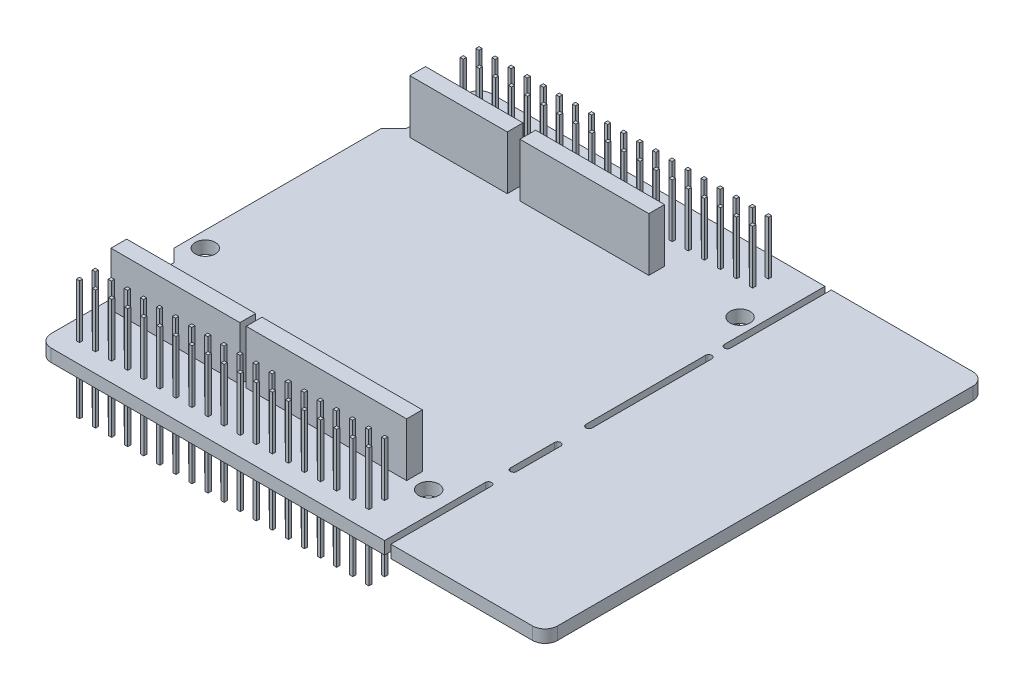
SolidWorks part; units mm, degrees
ref_plane "Płaszczyzna przednia" through (0, 0, 0) normal (0, 0, 1) x (1, 0, 0)
ref_plane "Płaszczyzna górna" through (0, 0, 0) normal (0, 1, 0) x (1, 0, 0)
ref_plane "Płaszczyzna prawa" through (0, 0, 0) normal (1, 0, 0) x (0, 0, -1)
sketch "Szkic2" plane through (0, 0, 0) normal (0, 1, 0) x (1, 0, 0)
  line L0 (-43.3193, -7.1981) -> (-41.3193, -9.1981)
  line L1 (-41.3193, -9.1981) -> (-41.3193, -28.6981)
  line L2 (-39.3193, -30.6981) -> (37.1807, -30.6981)
  line L3 (39.1807, -28.6981) -> (39.1807, 37.3019)
  line L4 (37.1807, 39.3019) -> (-39.3193, 39.3019)
  line L5 (-41.3193, 37.3019) -> (-41.3193, 27.8019)
  line L6 (-41.3193, 27.8019) -> (-43.3193, 25.8019)
  line L7 (-43.3193, 25.8019) -> (-43.3193, -7.1981)
  line L8 (14.1807, 39.3019) -> (14.1807, 23.3019) construction
  line L9 (14.6807, 39.3019) -> (14.6807, 23.3019)
  line L10 (13.6807, 39.3019) -> (13.6807, 23.3019)
  line L11 (14.1807, 20.3019) -> (14.1807, 1.3019) construction
  line L12 (14.6807, 20.3019) -> (14.6807, 1.3019)
  line L13 (13.6807, 20.3019) -> (13.6807, 1.3019)
  line L14 (14.1807, -3.6981) -> (14.1807, -10.6981) construction
  line L15 (14.6807, -3.6981) -> (14.6807, -10.6981)
  line L16 (13.6807, -3.6981) -> (13.6807, -10.6981)
  line L17 (14.1807, -14.6981) -> (14.1807, -30.6981) construction
  line L18 (14.6807, -14.6981) -> (14.6807, -30.6981)
  line L19 (13.6807, -14.6981) -> (13.6807, -30.6981)
  arc A0 (-41.3193, -28.6981) -> (-39.3193, -30.6981) centre (-39.3193, -28.6981) ccw
  arc A1 (37.1807, -30.6981) -> (39.1807, -28.6981) centre (37.1807, -28.6981) ccw
  arc A2 (39.1807, 37.3019) -> (37.1807, 39.3019) centre (37.1807, 37.3019) ccw
  arc A3 (-39.3193, 39.3019) -> (-41.3193, 37.3019) centre (-39.3193, 37.3019) ccw
  arc A4 (14.6807, 39.3019) -> (13.6807, 39.3019) centre (14.1807, 39.3019) ccw
  arc A5 (13.6807, 23.3019) -> (14.6807, 23.3019) centre (14.1807, 23.3019) ccw
  arc A6 (14.6807, 20.3019) -> (13.6807, 20.3019) centre (14.1807, 20.3019) ccw
  arc A7 (13.6807, 1.3019) -> (14.6807, 1.3019) centre (14.1807, 1.3019) ccw
  arc A8 (14.6807, -3.6981) -> (13.6807, -3.6981) centre (14.1807, -3.6981) ccw
  arc A9 (13.6807, -10.6981) -> (14.6807, -10.6981) centre (14.1807, -10.6981) ccw
  arc A10 (14.6807, -14.6981) -> (13.6807, -14.6981) centre (14.1807, -14.6981) ccw
  arc A11 (13.6807, -30.6981) -> (14.6807, -30.6981) centre (14.1807, -30.6981) ccw
  circle A12 centre (10.1807, -20.1981) radius 1.6
  circle A13 centre (11.1807, 28.3019) radius 1.6
  circle A14 centre (-40.8193, -4.6981) radius 1.6
  point P2 (14.1807, 31.3019)
  point P25 (14.1807, 10.8019)
  point P32 (14.1807, -7.1981)
  point P37 (14.1807, -22.6981)
  dimension "D4" = 2
  dimension "D8" = 1
  dimension "D16" = 3.2
  dimension "D1" = 80.5
  dimension "D2" = 70
  dimension "D3" = 82.5
  dimension "D5" = 11.5
  dimension "D6" = 135
  dimension "D7" = 21.5
  dimension "D9" = 24.5
  dimension "D10" = 16
  dimension "D11" = 19
  dimension "D12" = 3
  dimension "D13" = 5
  dimension "D14" = 7
  dimension "D15" = 4
  dimension "D17" = 2.5
  dimension "D18" = 26
  dimension "D19" = 10.5
  dimension "D20" = 53.5
  dimension "D21" = 54.5
  dimension "D22" = 11
extrude "Dodanie-wyciągnięcie1" add sketch "Szkic2" along normal blind 2 contours A10 L18 L2 A1 L3 A2 L4 L9 A5 L10 A3 L5 L6 L7 L0 L1 A0 L19 A14 A13 A12 A9 L16 A8 L15 A7 L13 A6 L12
sketch "Szkic3" plane through (0, 2, 0) normal (0, 1, 0) x (1, 0, 0)
  line L0 (-41.3193, -9.1981) -> (-41.3193, -28.6981) construction
  line L1 (-39.8193, 26.8019) -> (-24.3193, 26.8019)
  line L2 (-39.8193, 26.8019) -> (-39.8193, 29.3019)
  line L3 (-39.8193, 29.3019) -> (-24.3193, 29.3019)
  line L4 (-24.3193, 26.8019) -> (-24.3193, 29.3019)
  line L5 (-22.3193, 26.8019) -> (-1.8193, 26.8019)
  line L6 (-22.3193, 26.8019) -> (-22.3193, 29.3019)
  line L7 (-22.3193, 29.3019) -> (-1.8193, 29.3019)
  line L8 (-1.8193, 26.8019) -> (-1.8193, 29.3019)
  line L9 (-39.8193, -20.6981) -> (-19.3193, -20.6981)
  line L10 (-39.8193, -20.6981) -> (-39.8193, -18.1981)
  line L11 (-39.8193, -18.1981) -> (-19.3193, -18.1981)
  line L12 (-19.3193, -20.6981) -> (-19.3193, -18.1981)
  line L13 (-18.3193, -20.6981) -> (7.1807, -20.6981)
  line L14 (-18.3193, -20.6981) -> (-18.3193, -18.1981)
  line L15 (-18.3193, -18.1981) -> (7.1807, -18.1981)
  line L16 (7.1807, -20.6981) -> (7.1807, -18.1981)
  line L18 (13.6807, 39.3019) -> (-39.3193, 39.3019) construction
  line L19 (-39.3193, -30.6981) -> (13.6807, -30.6981) construction
  dimension "D1" = 2.5
  dimension "D2" = 15.5
  dimension "D3" = 2.5
  dimension "D4" = 20.5
  dimension "D5" = 2.5
  dimension "D6" = 20.5
  dimension "D7" = 2.5
  dimension "D8" = 25.5
  dimension "D9" = 1.5
  dimension "D10" = 1
  dimension "D11" = 2
  dimension "D12" = 10
  dimension "D13" = 10
extrude "Dodanie-wyciągnięcie2" add sketch "Szkic3" along normal blind 8.5
sketch "Szkic4" plane through (0, 0, 0) normal (0, -1, 0) x (-1, 0, 0)
  line L8 (-9.1807, 32.3019) -> (39.3193, 32.3019) construction
  line L9 (-9.1807, 32.3019) -> (-9.1807, 37.3019) construction
  line L10 (-9.1807, 37.3019) -> (39.3193, 37.3019) construction
  line L11 (39.3193, 32.3019) -> (39.3193, 37.3019) construction
  line L12 (-13.6807, 39.3019) -> (39.3193, 39.3019) construction
  line L165 (-9.1807, 34.8019) -> (39.3193, 34.8019) construction
  line L166 (-8.1807, 35.8019) -> (-7.6807, 35.8019)
  line L167 (-8.1807, 35.8019) -> (-8.1807, 36.3019)
  line L168 (-8.1807, 36.3019) -> (-7.6807, 36.3019)
  line L169 (-7.6807, 35.8019) -> (-7.6807, 36.3019)
  line L170 (-8.1807, 33.3019) -> (-7.6807, 33.3019)
  line L171 (-8.1807, 33.3019) -> (-8.1807, 33.8019)
  line L172 (-8.1807, 33.8019) -> (-7.6807, 33.8019)
  line L173 (-7.6807, 33.3019) -> (-7.6807, 33.8019)
  line L174 (-5.6251, 35.8019) -> (-5.6251, 36.3019)
  line L176 (-5.6251, 35.8019) -> (-5.1251, 35.8019)
  line L177 (-5.1251, 35.8019) -> (-5.1251, 36.3019)
  line L178 (-5.6251, 36.3019) -> (-5.1251, 36.3019)
  line L179 (-5.6251, 33.3019) -> (-5.6251, 33.8019)
  line L180 (-5.6251, 33.3019) -> (-5.1251, 33.3019)
  line L181 (-5.1251, 33.3019) -> (-5.1251, 33.8019)
  line L182 (-5.6251, 33.8019) -> (-5.1251, 33.8019)
  line L183 (-3.0696, 35.8019) -> (-3.0696, 36.3019)
  line L184 (-3.0696, 35.8019) -> (-2.5696, 35.8019)
  line L185 (-2.5696, 35.8019) -> (-2.5696, 36.3019)
  line L186 (-3.0696, 36.3019) -> (-2.5696, 36.3019)
  line L187 (-3.0696, 33.3019) -> (-3.0696, 33.8019)
  line L188 (-3.0696, 33.3019) -> (-2.5696, 33.3019)
  line L189 (-2.5696, 33.3019) -> (-2.5696, 33.8019)
  line L190 (-3.0696, 33.8019) -> (-2.5696, 33.8019)
  line L191 (-0.514, 35.8019) -> (-0.514, 36.3019)
  line L192 (-0.514, 35.8019) -> (-0.014, 35.8019)
  line L193 (-0.014, 35.8019) -> (-0.014, 36.3019)
  line L194 (-0.514, 36.3019) -> (-0.014, 36.3019)
  line L195 (-0.514, 33.3019) -> (-0.514, 33.8019)
  line L196 (-0.514, 33.3019) -> (-0.014, 33.3019)
  line L197 (-0.014, 33.3019) -> (-0.014, 33.8019)
  line L198 (-0.514, 33.8019) -> (-0.014, 33.8019)
  line L199 (2.0415, 35.8019) -> (2.0415, 36.3019)
  line L200 (2.0415, 35.8019) -> (2.5415, 35.8019)
  line L201 (2.5415, 35.8019) -> (2.5415, 36.3019)
  line L202 (2.0415, 36.3019) -> (2.5415, 36.3019)
  line L203 (2.0415, 33.3019) -> (2.0415, 33.8019)
  line L204 (2.0415, 33.3019) -> (2.5415, 33.3019)
  line L205 (2.5415, 33.3019) -> (2.5415, 33.8019)
  line L206 (2.0415, 33.8019) -> (2.5415, 33.8019)
  line L207 (4.5971, 35.8019) -> (4.5971, 36.3019)
  line L208 (4.5971, 35.8019) -> (5.0971, 35.8019)
  line L209 (5.0971, 35.8019) -> (5.0971, 36.3019)
  line L210 (4.5971, 36.3019) -> (5.0971, 36.3019)
  line L211 (4.5971, 33.3019) -> (4.5971, 33.8019)
  line L212 (4.5971, 33.3019) -> (5.0971, 33.3019)
  line L213 (5.0971, 33.3019) -> (5.0971, 33.8019)
  line L214 (4.5971, 33.8019) -> (5.0971, 33.8019)
  line L215 (7.1526, 35.8019) -> (7.1526, 36.3019)
  line L216 (7.1526, 35.8019) -> (7.6526, 35.8019)
  line L217 (7.6526, 35.8019) -> (7.6526, 36.3019)
  line L218 (7.1526, 36.3019) -> (7.6526, 36.3019)
  line L219 (7.1526, 33.3019) -> (7.1526, 33.8019)
  line L220 (7.1526, 33.3019) -> (7.6526, 33.3019)
  line L221 (7.6526, 33.3019) -> (7.6526, 33.8019)
  line L222 (7.1526, 33.8019) -> (7.6526, 33.8019)
  line L223 (9.7082, 35.8019) -> (9.7082, 36.3019)
  line L224 (9.7082, 35.8019) -> (10.2082, 35.8019)
  line L225 (10.2082, 35.8019) -> (10.2082, 36.3019)
  line L226 (9.7082, 36.3019) -> (10.2082, 36.3019)
  line L227 (9.7082, 33.3019) -> (9.7082, 33.8019)
  line L228 (9.7082, 33.3019) -> (10.2082, 33.3019)
  line L229 (10.2082, 33.3019) -> (10.2082, 33.8019)
  line L230 (9.7082, 33.8019) -> (10.2082, 33.8019)
  line L231 (12.2637, 35.8019) -> (12.2637, 36.3019)
  line L232 (12.2637, 35.8019) -> (12.7637, 35.8019)
  line L233 (12.7637, 35.8019) -> (12.7637, 36.3019)
  line L234 (12.2637, 36.3019) -> (12.7637, 36.3019)
  line L235 (12.2637, 33.3019) -> (12.2637, 33.8019)
  line L236 (12.2637, 33.3019) -> (12.7637, 33.3019)
  line L237 (12.7637, 33.3019) -> (12.7637, 33.8019)
  line L238 (12.2637, 33.8019) -> (12.7637, 33.8019)
  line L239 (14.8193, 35.8019) -> (14.8193, 36.3019)
  line L240 (14.8193, 35.8019) -> (15.3193, 35.8019)
  line L241 (15.3193, 35.8019) -> (15.3193, 36.3019)
  line L242 (14.8193, 36.3019) -> (15.3193, 36.3019)
  line L243 (14.8193, 33.3019) -> (14.8193, 33.8019)
  line L244 (14.8193, 33.3019) -> (15.3193, 33.3019)
  line L245 (15.3193, 33.3019) -> (15.3193, 33.8019)
  line L246 (14.8193, 33.8019) -> (15.3193, 33.8019)
  line L247 (17.3749, 35.8019) -> (17.3749, 36.3019)
  line L248 (17.3749, 35.8019) -> (17.8749, 35.8019)
  line L249 (17.8749, 35.8019) -> (17.8749, 36.3019)
  line L250 (17.3749, 36.3019) -> (17.8749, 36.3019)
  line L251 (17.3749, 33.3019) -> (17.3749, 33.8019)
  line L252 (17.3749, 33.3019) -> (17.8749, 33.3019)
  line L253 (17.8749, 33.3019) -> (17.8749, 33.8019)
  line L254 (17.3749, 33.8019) -> (17.8749, 33.8019)
  line L255 (19.9304, 35.8019) -> (19.9304, 36.3019)
  line L256 (19.9304, 35.8019) -> (20.4304, 35.8019)
  line L257 (20.4304, 35.8019) -> (20.4304, 36.3019)
  line L258 (19.9304, 36.3019) -> (20.4304, 36.3019)
  line L259 (19.9304, 33.3019) -> (19.9304, 33.8019)
  line L260 (19.9304, 33.3019) -> (20.4304, 33.3019)
  line L261 (20.4304, 33.3019) -> (20.4304, 33.8019)
  line L262 (19.9304, 33.8019) -> (20.4304, 33.8019)
  line L263 (22.486, 35.8019) -> (22.486, 36.3019)
  line L264 (22.486, 35.8019) -> (22.986, 35.8019)
  line L265 (22.986, 35.8019) -> (22.986, 36.3019)
  line L266 (22.486, 36.3019) -> (22.986, 36.3019)
  line L267 (22.486, 33.3019) -> (22.486, 33.8019)
  line L268 (22.486, 33.3019) -> (22.986, 33.3019)
  line L269 (22.986, 33.3019) -> (22.986, 33.8019)
  line L270 (22.486, 33.8019) -> (22.986, 33.8019)
  line L271 (25.0415, 35.8019) -> (25.0415, 36.3019)
  line L272 (25.0415, 35.8019) -> (25.5415, 35.8019)
  line L273 (25.5415, 35.8019) -> (25.5415, 36.3019)
  line L274 (25.0415, 36.3019) -> (25.5415, 36.3019)
  line L275 (25.0415, 33.3019) -> (25.0415, 33.8019)
  line L276 (25.0415, 33.3019) -> (25.5415, 33.3019)
  line L277 (25.5415, 33.3019) -> (25.5415, 33.8019)
  line L278 (25.0415, 33.8019) -> (25.5415, 33.8019)
  line L279 (27.5971, 35.8019) -> (27.5971, 36.3019)
  line L280 (27.5971, 35.8019) -> (28.0971, 35.8019)
  line L281 (28.0971, 35.8019) -> (28.0971, 36.3019)
  line L282 (27.5971, 36.3019) -> (28.0971, 36.3019)
  line L283 (27.5971, 33.3019) -> (27.5971, 33.8019)
  line L284 (27.5971, 33.3019) -> (28.0971, 33.3019)
  line L285 (28.0971, 33.3019) -> (28.0971, 33.8019)
  line L286 (27.5971, 33.8019) -> (28.0971, 33.8019)
  line L287 (30.1526, 35.8019) -> (30.1526, 36.3019)
  line L288 (30.1526, 35.8019) -> (30.6526, 35.8019)
  line L289 (30.6526, 35.8019) -> (30.6526, 36.3019)
  line L290 (30.1526, 36.3019) -> (30.6526, 36.3019)
  line L291 (30.1526, 33.3019) -> (30.1526, 33.8019)
  line L292 (30.1526, 33.3019) -> (30.6526, 33.3019)
  line L293 (30.6526, 33.3019) -> (30.6526, 33.8019)
  line L294 (30.1526, 33.8019) -> (30.6526, 33.8019)
  line L295 (32.7082, 35.8019) -> (32.7082, 36.3019)
  line L296 (32.7082, 35.8019) -> (33.2082, 35.8019)
  line L297 (33.2082, 35.8019) -> (33.2082, 36.3019)
  line L298 (32.7082, 36.3019) -> (33.2082, 36.3019)
  line L299 (32.7082, 33.3019) -> (32.7082, 33.8019)
  line L300 (32.7082, 33.3019) -> (33.2082, 33.3019)
  line L301 (33.2082, 33.3019) -> (33.2082, 33.8019)
  line L302 (32.7082, 33.8019) -> (33.2082, 33.8019)
  line L303 (35.2637, 35.8019) -> (35.2637, 36.3019)
  line L304 (35.2637, 35.8019) -> (35.7637, 35.8019)
  line L305 (35.7637, 35.8019) -> (35.7637, 36.3019)
  line L306 (35.2637, 36.3019) -> (35.7637, 36.3019)
  line L307 (35.2637, 33.3019) -> (35.2637, 33.8019)
  line L308 (35.2637, 33.3019) -> (35.7637, 33.3019)
  line L309 (35.7637, 33.3019) -> (35.7637, 33.8019)
  line L310 (35.2637, 33.8019) -> (35.7637, 33.8019)
  line L311 (37.8193, 35.8019) -> (37.8193, 36.3019)
  line L312 (37.8193, 35.8019) -> (38.3193, 35.8019)
  line L313 (38.3193, 35.8019) -> (38.3193, 36.3019)
  line L314 (37.8193, 36.3019) -> (38.3193, 36.3019)
  line L315 (37.8193, 33.3019) -> (37.8193, 33.8019)
  line L316 (37.8193, 33.3019) -> (38.3193, 33.3019)
  line L317 (38.3193, 33.3019) -> (38.3193, 33.8019)
  line L318 (37.8193, 33.8019) -> (38.3193, 33.8019)
  line L319 (-9.1807, -28.6981) -> (39.3193, -28.6981) construction
  line L320 (-9.1807, -28.6981) -> (-9.1807, -23.6981) construction
  line L321 (-9.1807, -23.6981) -> (39.3193, -23.6981) construction
  line L322 (39.3193, -28.6981) -> (39.3193, -23.6981) construction
  line L323 (-9.1807, -26.1981) -> (39.3193, -26.1981) construction
  line L324 (-8.1807, -25.1981) -> (-7.6807, -25.1981)
  line L325 (-8.1807, -25.1981) -> (-8.1807, -24.6981)
  line L326 (-8.1807, -24.6981) -> (-7.6807, -24.6981)
  line L327 (-7.6807, -25.1981) -> (-7.6807, -24.6981)
  line L328 (-8.1807, -27.6981) -> (-7.6807, -27.6981)
  line L329 (-8.1807, -27.6981) -> (-8.1807, -27.1981)
  line L330 (-8.1807, -27.1981) -> (-7.6807, -27.1981)
  line L331 (-7.6807, -27.6981) -> (-7.6807, -27.1981)
  line L332 (-5.6251, -25.1981) -> (-5.6251, -24.6981)
  line L333 (-5.6251, -25.1981) -> (-5.1251, -25.1981)
  line L334 (-5.1251, -25.1981) -> (-5.1251, -24.6981)
  line L335 (-5.6251, -24.6981) -> (-5.1251, -24.6981)
  line L336 (-5.6251, -27.6981) -> (-5.6251, -27.1981)
  line L337 (-5.6251, -27.6981) -> (-5.1251, -27.6981)
  line L338 (-5.1251, -27.6981) -> (-5.1251, -27.1981)
  line L339 (-5.6251, -27.1981) -> (-5.1251, -27.1981)
  line L340 (-3.0696, -25.1981) -> (-3.0696, -24.6981)
  line L341 (-3.0696, -25.1981) -> (-2.5696, -25.1981)
  line L342 (-2.5696, -25.1981) -> (-2.5696, -24.6981)
  line L343 (-3.0696, -24.6981) -> (-2.5696, -24.6981)
  line L344 (-3.0696, -27.6981) -> (-3.0696, -27.1981)
  line L345 (-3.0696, -27.6981) -> (-2.5696, -27.6981)
  line L346 (-2.5696, -27.6981) -> (-2.5696, -27.1981)
  line L347 (-3.0696, -27.1981) -> (-2.5696, -27.1981)
  line L348 (-0.514, -25.1981) -> (-0.514, -24.6981)
  line L349 (-0.514, -25.1981) -> (-0.014, -25.1981)
  line L350 (-0.014, -25.1981) -> (-0.014, -24.6981)
  line L351 (-0.514, -24.6981) -> (-0.014, -24.6981)
  line L352 (-0.514, -27.6981) -> (-0.514, -27.1981)
  line L353 (-0.514, -27.6981) -> (-0.014, -27.6981)
  line L354 (-0.014, -27.6981) -> (-0.014, -27.1981)
  line L355 (-0.514, -27.1981) -> (-0.014, -27.1981)
  line L356 (2.0415, -25.1981) -> (2.0415, -24.6981)
  line L357 (2.0415, -25.1981) -> (2.5415, -25.1981)
  line L358 (2.5415, -25.1981) -> (2.5415, -24.6981)
  line L359 (2.0415, -24.6981) -> (2.5415, -24.6981)
  line L360 (2.0415, -27.6981) -> (2.0415, -27.1981)
  line L361 (2.0415, -27.6981) -> (2.5415, -27.6981)
  line L362 (2.5415, -27.6981) -> (2.5415, -27.1981)
  line L363 (2.0415, -27.1981) -> (2.5415, -27.1981)
  line L364 (4.5971, -25.1981) -> (4.5971, -24.6981)
  line L365 (4.5971, -25.1981) -> (5.0971, -25.1981)
  line L366 (5.0971, -25.1981) -> (5.0971, -24.6981)
  line L367 (4.5971, -24.6981) -> (5.0971, -24.6981)
  line L368 (4.5971, -27.6981) -> (4.5971, -27.1981)
  line L369 (4.5971, -27.6981) -> (5.0971, -27.6981)
  line L370 (5.0971, -27.6981) -> (5.0971, -27.1981)
  line L371 (4.5971, -27.1981) -> (5.0971, -27.1981)
  line L372 (7.1526, -25.1981) -> (7.1526, -24.6981)
  line L373 (7.1526, -25.1981) -> (7.6526, -25.1981)
  line L374 (7.6526, -25.1981) -> (7.6526, -24.6981)
  line L375 (7.1526, -24.6981) -> (7.6526, -24.6981)
  line L376 (7.1526, -27.6981) -> (7.1526, -27.1981)
  line L377 (7.1526, -27.6981) -> (7.6526, -27.6981)
  line L378 (7.6526, -27.6981) -> (7.6526, -27.1981)
  line L379 (7.1526, -27.1981) -> (7.6526, -27.1981)
  line L380 (9.7082, -25.1981) -> (9.7082, -24.6981)
  line L381 (9.7082, -25.1981) -> (10.2082, -25.1981)
  line L382 (10.2082, -25.1981) -> (10.2082, -24.6981)
  line L383 (9.7082, -24.6981) -> (10.2082, -24.6981)
  line L384 (9.7082, -27.6981) -> (9.7082, -27.1981)
  line L385 (9.7082, -27.6981) -> (10.2082, -27.6981)
  line L386 (10.2082, -27.6981) -> (10.2082, -27.1981)
  line L387 (9.7082, -27.1981) -> (10.2082, -27.1981)
  line L388 (12.2637, -25.1981) -> (12.2637, -24.6981)
  line L389 (12.2637, -25.1981) -> (12.7637, -25.1981)
  line L390 (12.7637, -25.1981) -> (12.7637, -24.6981)
  line L391 (12.2637, -24.6981) -> (12.7637, -24.6981)
  line L392 (12.2637, -27.6981) -> (12.2637, -27.1981)
  line L393 (12.2637, -27.6981) -> (12.7637, -27.6981)
  line L394 (12.7637, -27.6981) -> (12.7637, -27.1981)
  line L395 (12.2637, -27.1981) -> (12.7637, -27.1981)
  line L396 (14.8193, -25.1981) -> (14.8193, -24.6981)
  line L397 (14.8193, -25.1981) -> (15.3193, -25.1981)
  line L398 (15.3193, -25.1981) -> (15.3193, -24.6981)
  line L399 (14.8193, -24.6981) -> (15.3193, -24.6981)
  line L400 (14.8193, -27.6981) -> (14.8193, -27.1981)
  line L401 (14.8193, -27.6981) -> (15.3193, -27.6981)
  line L402 (15.3193, -27.6981) -> (15.3193, -27.1981)
  line L403 (14.8193, -27.1981) -> (15.3193, -27.1981)
  line L404 (17.3749, -25.1981) -> (17.3749, -24.6981)
  line L405 (17.3749, -25.1981) -> (17.8749, -25.1981)
  line L406 (17.8749, -25.1981) -> (17.8749, -24.6981)
  line L407 (17.3749, -24.6981) -> (17.8749, -24.6981)
  line L408 (17.3749, -27.6981) -> (17.3749, -27.1981)
  line L409 (17.3749, -27.6981) -> (17.8749, -27.6981)
  line L410 (17.8749, -27.6981) -> (17.8749, -27.1981)
  line L411 (17.3749, -27.1981) -> (17.8749, -27.1981)
  line L412 (19.9304, -25.1981) -> (19.9304, -24.6981)
  line L413 (19.9304, -25.1981) -> (20.4304, -25.1981)
  line L414 (20.4304, -25.1981) -> (20.4304, -24.6981)
  line L415 (19.9304, -24.6981) -> (20.4304, -24.6981)
  line L416 (19.9304, -27.6981) -> (19.9304, -27.1981)
  line L417 (19.9304, -27.6981) -> (20.4304, -27.6981)
  line L418 (20.4304, -27.6981) -> (20.4304, -27.1981)
  line L419 (19.9304, -27.1981) -> (20.4304, -27.1981)
  line L420 (22.486, -25.1981) -> (22.486, -24.6981)
  line L421 (22.486, -25.1981) -> (22.986, -25.1981)
  line L422 (22.986, -25.1981) -> (22.986, -24.6981)
  line L423 (22.486, -24.6981) -> (22.986, -24.6981)
  line L424 (22.486, -27.6981) -> (22.486, -27.1981)
  line L425 (22.486, -27.6981) -> (22.986, -27.6981)
  line L426 (22.986, -27.6981) -> (22.986, -27.1981)
  line L427 (22.486, -27.1981) -> (22.986, -27.1981)
  line L428 (25.0415, -25.1981) -> (25.0415, -24.6981)
  line L429 (25.0415, -25.1981) -> (25.5415, -25.1981)
  line L430 (25.5415, -25.1981) -> (25.5415, -24.6981)
  line L431 (25.0415, -24.6981) -> (25.5415, -24.6981)
  line L432 (25.0415, -27.6981) -> (25.0415, -27.1981)
  line L433 (25.0415, -27.6981) -> (25.5415, -27.6981)
  line L434 (25.5415, -27.6981) -> (25.5415, -27.1981)
  line L435 (25.0415, -27.1981) -> (25.5415, -27.1981)
  line L436 (27.5971, -25.1981) -> (27.5971, -24.6981)
  line L437 (27.5971, -25.1981) -> (28.0971, -25.1981)
  line L438 (28.0971, -25.1981) -> (28.0971, -24.6981)
  line L439 (27.5971, -24.6981) -> (28.0971, -24.6981)
  line L440 (27.5971, -27.6981) -> (27.5971, -27.1981)
  line L441 (27.5971, -27.6981) -> (28.0971, -27.6981)
  line L442 (28.0971, -27.6981) -> (28.0971, -27.1981)
  line L443 (27.5971, -27.1981) -> (28.0971, -27.1981)
  line L444 (30.1526, -25.1981) -> (30.1526, -24.6981)
  line L445 (30.1526, -25.1981) -> (30.6526, -25.1981)
  line L446 (30.6526, -25.1981) -> (30.6526, -24.6981)
  line L447 (30.1526, -24.6981) -> (30.6526, -24.6981)
  line L448 (30.1526, -27.6981) -> (30.1526, -27.1981)
  line L449 (30.1526, -27.6981) -> (30.6526, -27.6981)
  line L450 (30.6526, -27.6981) -> (30.6526, -27.1981)
  line L451 (30.1526, -27.1981) -> (30.6526, -27.1981)
  line L452 (32.7082, -25.1981) -> (32.7082, -24.6981)
  line L453 (32.7082, -25.1981) -> (33.2082, -25.1981)
  line L454 (33.2082, -25.1981) -> (33.2082, -24.6981)
  line L455 (32.7082, -24.6981) -> (33.2082, -24.6981)
  line L456 (32.7082, -27.6981) -> (32.7082, -27.1981)
  line L457 (32.7082, -27.6981) -> (33.2082, -27.6981)
  line L458 (33.2082, -27.6981) -> (33.2082, -27.1981)
  line L459 (32.7082, -27.1981) -> (33.2082, -27.1981)
  line L460 (35.2637, -25.1981) -> (35.2637, -24.6981)
  line L461 (35.2637, -25.1981) -> (35.7637, -25.1981)
  line L462 (35.7637, -25.1981) -> (35.7637, -24.6981)
  line L463 (35.2637, -24.6981) -> (35.7637, -24.6981)
  line L464 (35.2637, -27.6981) -> (35.2637, -27.1981)
  line L465 (35.2637, -27.6981) -> (35.7637, -27.6981)
  line L466 (35.7637, -27.6981) -> (35.7637, -27.1981)
  line L467 (35.2637, -27.1981) -> (35.7637, -27.1981)
  line L468 (37.8193, -25.1981) -> (37.8193, -24.6981)
  line L469 (37.8193, -25.1981) -> (38.3193, -25.1981)
  line L470 (38.3193, -25.1981) -> (38.3193, -24.6981)
  line L471 (37.8193, -24.6981) -> (38.3193, -24.6981)
  line L472 (37.8193, -27.6981) -> (37.8193, -27.1981)
  line L473 (37.8193, -27.6981) -> (38.3193, -27.6981)
  line L474 (38.3193, -27.6981) -> (38.3193, -27.1981)
  line L475 (37.8193, -27.1981) -> (38.3193, -27.1981)
  line L476 (41.3193, -9.1981) -> (41.3193, -28.6981) construction
  line L477 (39.3193, -30.6981) -> (-13.6807, -30.6981) construction
  point P0 (39.3193, -28.6981)
  point P177 (38.0693, 34.8019)
  point P329 (38.0693, -26.1981)
  dimension "D5" = 5
  dimension "D6" = 48.5
  dimension "D7" = 2
  dimension "D11" = 0.5
  dimension "D12" = 0.5
  dimension "D13" = 1
  dimension "D14" = 1
  dimension "D15" = 1
  dimension "D16" = 1
  dimension "D17" = 1
  dimension "D18" = 1.25
  dimension "D8" = 48.5
  dimension "D9" = 0.5
  dimension "D10" = 0.5
  dimension "D19" = 1
  dimension "D20" = 1
  dimension "D21" = 1
  dimension "D22" = 1
  dimension "D23" = 1
  dimension "D3" = 2
  dimension "D4" = 2
extrude "Dodanie-wyciągnięcie3" add sketch "Szkic4" along normal blind 8.5 and the other way up to surface (10.5 mm away) other way up to face at (-32.0693, 10.5, -28.0519)
equation "\"D14@Szkic4\"=\"D13@Szkic4\""
